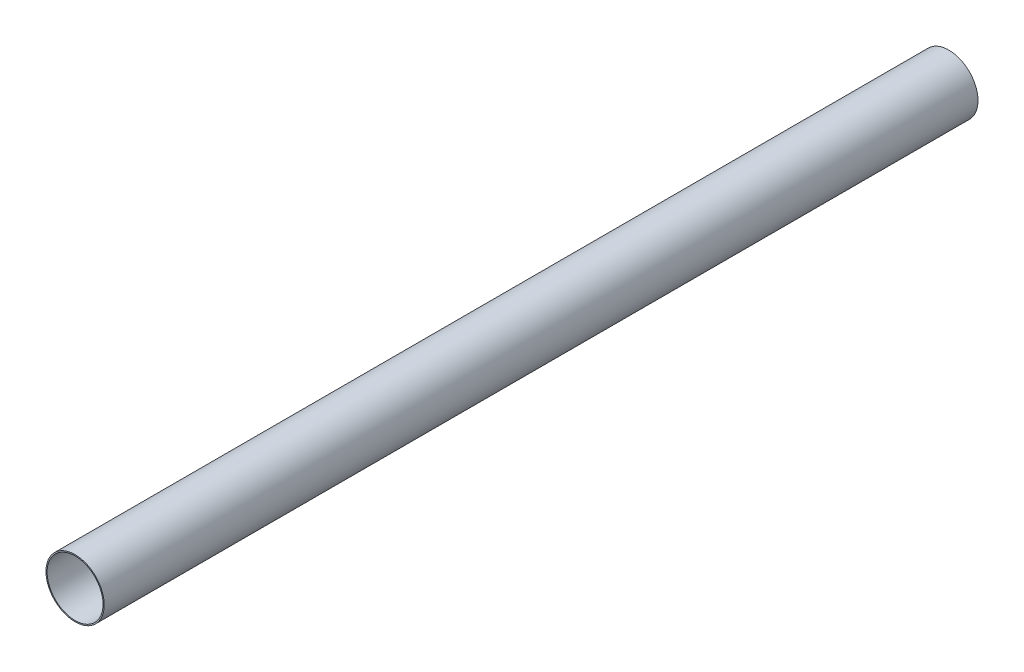
SolidWorks part; units mm, degrees
ref_plane "Front Plane" through (0, 0, 0) normal (0, 0, 1) x (1, 0, 0)
ref_plane "Top Plane" through (0, 0, 0) normal (0, 1, 0) x (1, 0, 0)
ref_plane "Right Plane" through (0, 0, 0) normal (1, 0, 0) x (0, 0, -1)
sketch "Sketch1" plane through (0, 0, 0) normal (0, 0, 1) x (1, 0, 0)
  circle A0 centre (0, 0) radius 48.8061
  circle A1 centre (0, 0) radius 50.8
  dimension "D1" = 97.6122
  dimension "D2" = 101.6
extrude "Boss-Extrude1" add sketch "Sketch1" along normal blind 1524
